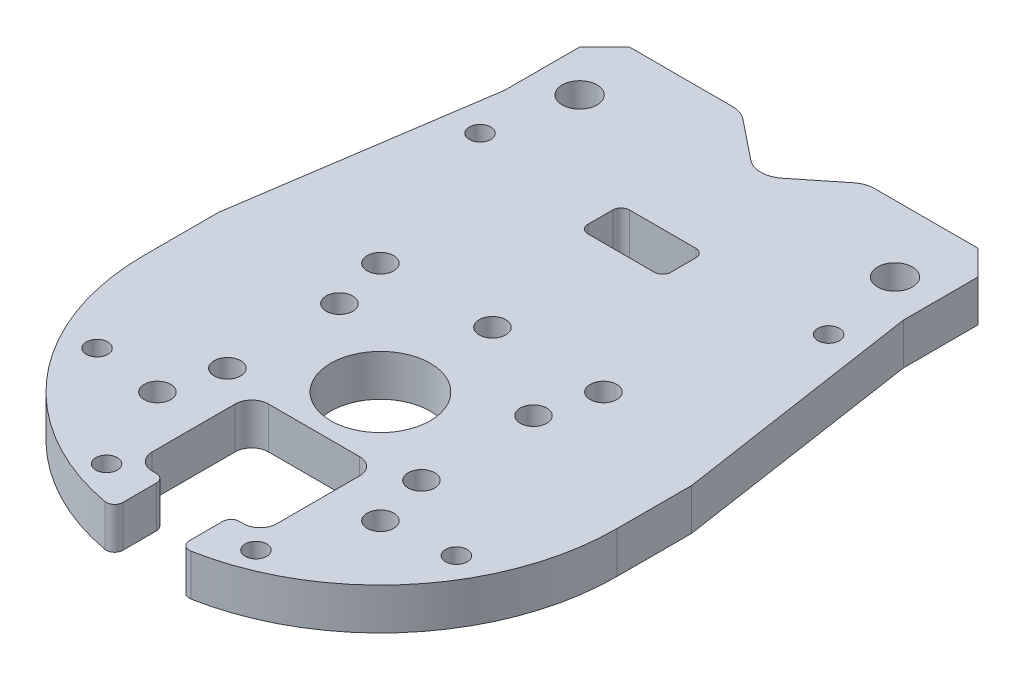
SolidWorks part; units mm, degrees
material "1060 合金"
ref_plane "前视基准面" through (0, 0, 0) normal (0, 0, 1) x (1, 0, 0)
ref_plane "上视基准面" through (0, 0, 0) normal (0, 1, 0) x (1, 0, 0)
ref_plane "右视基准面" through (0, 0, 0) normal (1, 0, 0) x (0, 0, -1)
other "Configuration Table"
sketch "草图1" plane through (0, 0, 0) normal (0, 1, 0) x (1, 0, 0)
  line L1 (-28.5, 0) -> (28.5, 0)
  line L2 (-28.5, 0) -> (-28.5, -51)
  line L4 (28.5, 0) -> (28.5, -51)
  arc A0 (-28.5, -51) -> (28.5, -51) centre (0, -51) ccw
  point P4 (0, 0)
  dimension "D1" = 57
  dimension "D2" = 51
extrude "凸台-拉伸1" add sketch "草图1" along normal blind 5
hole_wizard "M5 螺纹孔1" positions "3D草图1" profile "草图2" tap size "M5" standard "GB" end condition up to next
sketch3d "3D草图1"
  circle A0 centre (-19, 13, 8) radius 2.75 construction
  circle A1 centre (19, 13, 8) radius 2.75 construction
  point P0 (19, 5, 8)
  point P2 (-19, 5, 8)
  point P6 (-19, 15.75, 8)
  point P10 (19, 15.75, 8)
sketch "草图2" plane through (19, 5, 8) normal (1, 0, 0) x (0, 0, 1)
  line L0 (0, 0) -> (0, 5)
  line L1 (0, 5) -> (2.1, 5)
  line L2 (2.1, 5) -> (2.1, 0)
  line L5 (2.1, 0) -> (0, 0)
  line L11 (0, -6.35) -> (0, 107.95) construction
  dimension "通孔螺纹孔钻头直径" = 4.2
  dimension "通孔螺纹孔钻头深度" = 5
cosmetic thread "孔螺蚊线1" parameters "D2"=5
cosmetic thread "孔螺蚊线2" parameters "D2"=5
sketch "草图4" plane through (0, 0, 0) normal (0, -1, 0) x (1, 0, 0)
  line L0 (-13.435, 64.435) -> (0, 51) construction
  line L1 (0, 51) -> (0, 59.8826) construction
  circle A0 centre (0, 51) radius 19 construction
  circle A1 centre (-13.435, 64.435) radius 1.6
  circle A2 centre (13.435, 64.435) radius 1.6
  circle A3 centre (13.435, 37.565) radius 1.6
  circle A4 centre (-13.435, 37.565) radius 1.6
  point P17 (0, 51)
  dimension "D1" = 38
  dimension "D2" = 45
  dimension "D3" = 3.2
  dimension "D4" = 4
extrude "切除-拉伸1" cut sketch "草图4" against normal blind 10
sketch "草图5" plane through (0, 0, 0) normal (0, -1, 0) x (1, 0, 0)
  circle A0 centre (0, 51) radius 13.5 construction
  arc A1 (28.5, 51) -> (-28.5, 51) centre (0, 51) ccw construction
  circle A2 centre (0, 64.5) radius 1.6
  circle A3 centre (-13.435, 64.435) radius 1.6 construction
  circle A4 centre (11.6913, 57.75) radius 1.6
  circle A5 centre (11.6913, 44.25) radius 1.6
  circle A6 centre (0, 37.5) radius 1.6
  circle A7 centre (-11.6913, 44.25) radius 1.6
  circle A8 centre (-11.6913, 57.75) radius 1.6
  point P21 (0, 51)
  dimension "D1" = 27
  dimension "D2" = 6
extrude "切除-拉伸2" cut sketch "草图5" against normal blind 10
sketch "草图6" plane through (0, 0, 0) normal (0, -1, 0) x (1, 0, 0)
  circle A0 centre (0, 51) radius 6
  dimension "D1" = 12
extrude "切除-拉伸3" cut sketch "草图6" against normal blind 10
chamfer "倒角1" distance 2 angle 45 2 edges at (28.5, 2.5, 0) (-28.5, 2.5, 0)
sketch "草图7" plane through (0, 5, 0) normal (0, 1, 0) x (1, 0, 0)
  line L0 (-24, 0) -> (-24, -12)
  line L1 (26.5, 0) -> (-26.5, 0) construction
  line L2 (-24, -12) -> (-28.5, -42)
  line L3 (-28.5, -2) -> (-28.5, -51) construction
  line L4 (-24, 0) -> (-26.5, 0)
  line L5 (-26.5, 0) -> (-28.5, -2)
  line L6 (-28.5, -2) -> (-28.5, -42)
  line L7 (0, -2.2) -> (0, 2.2) construction
  line L8 (28.5, -2) -> (28.5, -42)
  line L9 (26.5, 0) -> (28.5, -2)
  line L10 (24, 0) -> (26.5, 0)
  line L11 (24, -12) -> (28.5, -42)
  line L12 (24, 0) -> (24, -12)
  dimension "D1" = 42
  dimension "D2" = 48
  dimension "D3" = 12
extrude "切除-拉伸4" cut sketch "草图7" against normal through all
chamfer "倒角2" distance 3 angle 45 2 edges at (24, 2.5, 0) (-24, 2.5, 0)
sketch "草图8" plane through (0, 5, 0) normal (0, 1, 0) x (1, 0, 0)
  circle A0 centre (0, -76) radius 1.3 construction
  circle A1 centre (-21.6506, -63.5) radius 1.3
  circle A2 centre (-21.6506, -38.5) radius 1.3 construction
  circle A3 centre (0, -26) radius 1.3 construction
  circle A4 centre (21.6506, -38.5) radius 1.3 construction
  circle A5 centre (21.6506, -63.5) radius 1.3
  point P3 (0, -51)
  point P16 (0, -51)
  dimension "D2" = 2.6
  dimension "D1" = 25
  dimension "D3" = 6
extrude "切除-拉伸5" cut sketch "草图8" against normal through all
sketch "草图9" plane through (0, 5, 0) normal (0, 1, 0) x (1, 0, 0)
  line L0 (0, -2.75) -> (0, 2.75) construction
  line L1 (21, 0) -> (-21, 0) construction
  circle A0 centre (-21, -18) radius 1.3
  circle A1 centre (21, -18) radius 1.3
  circle A2 centre (-21.6506, -63.5) radius 1.3 construction
  dimension "D2" = 42
  dimension "D1" = 18
extrude "切除-拉伸6" cut sketch "草图9" against normal through all
sketch "草图11" plane through (0, 5, 0) normal (0, 1, 0) x (1, 0, 0)
  line L0 (-7.5, 0) -> (0, -6)
  line L1 (21, 0) -> (-21, 0) construction
  line L2 (0, -2.2) -> (0, 2.2) construction
  line L3 (7.5, 0) -> (0, -6)
  line L4 (-7.5, 0) -> (7.5, 0)
  dimension "D1" = 15
  dimension "D2" = 6
extrude "切除-拉伸8" cut sketch "草图11" against normal blind 10
fillet "圆角1" radius 3 3 edges at (7.5, 2.5, 0) (-7.5, 2.5, 0) (0, 2.5, 6)
sketch "草图12" plane through (0, 5, 0) normal (0, 1, 0) x (1, 0, 0)
  line L1 (-7.5, -59) -> (7.5, -59)
  line L2 (-7.5, -59) -> (-7.5, -73)
  line L3 (-7.5, -73) -> (7.5, -73)
  line L4 (7.5, -59) -> (7.5, -73)
  circle A0 centre (0, -51) radius 6 construction
  point P6 (0, -59)
  dimension "D1" = 2
  dimension "D2" = 14
  dimension "D3" = 15
extrude "切除-拉伸9" cut sketch "草图12" against normal blind 10
fillet "圆角2" radius 2 4 edges at (7.5, 2.5, 73) (-7.5, 2.5, 73) (-7.5, 2.5, 59) (7.5, 2.5, 59)
sketch "草图13" plane through (0, 0, 0) normal (0, -1, 0) x (1, 0, 0)
  line L0 (-5.5, 73) -> (5.5, 73) construction
  line L1 (-4, 73) -> (4, 73)
  line L2 (-4, 73) -> (-4, 79.5)
  line L3 (-4, 79.5) -> (4, 79.5)
  line L4 (4, 73) -> (4, 79.5)
  arc A0 (28.5, 51) -> (-28.5, 51) centre (0, 51) ccw construction
  point P9 (0, 79.5)
  dimension "D1" = 8
extrude "切除-拉伸10" cut sketch "草图13" against normal blind 10
fillet "圆角3" radius 1 4 edges at (-4, 2.5, 73) (4, 2.5, 73) (4, 2.5, 79.2179) (-4, 2.5, 79.2179)
sketch "草图14" plane through (0, 0, 0) normal (0, -1, 0) x (1, 0, 0)
  line L0 (0, -2.75) -> (0, 2.75) construction
  line L1 (-8.5523, 0) -> (-21, 0) construction
  circle A0 centre (-9, 75) radius 1.3
  circle A2 centre (9, 75) radius 1.3
  circle A5 centre (-21.6506, 63.5) radius 1.3 construction
  dimension "D1" = 18
  dimension "D2" = 75
extrude "切除-拉伸11" cut sketch "草图14" against normal blind 10 contours A0
sketch "草图15" plane through (0, 5, 0) normal (0, 1, 0) x (1, 0, 0)
  line L0 (-8.5523, 0) -> (-21, 0) construction
  line L1 (-5, -17) -> (5, -17)
  line L2 (-5, -17) -> (-5, -22)
  line L3 (-5, -22) -> (5, -22)
  line L4 (5, -17) -> (5, -22)
  point P4 (0, -17)
  dimension "D1" = 17
  dimension "D2" = 10
  dimension "D3" = 5
extrude "切除-拉伸12" cut sketch "草图15" against normal blind 10
fillet "圆角4" radius 1 4 edges at (5, 2.5, 22) (-5, 2.5, 22) (5, 2.5, 17) (-5, 2.5, 17)
